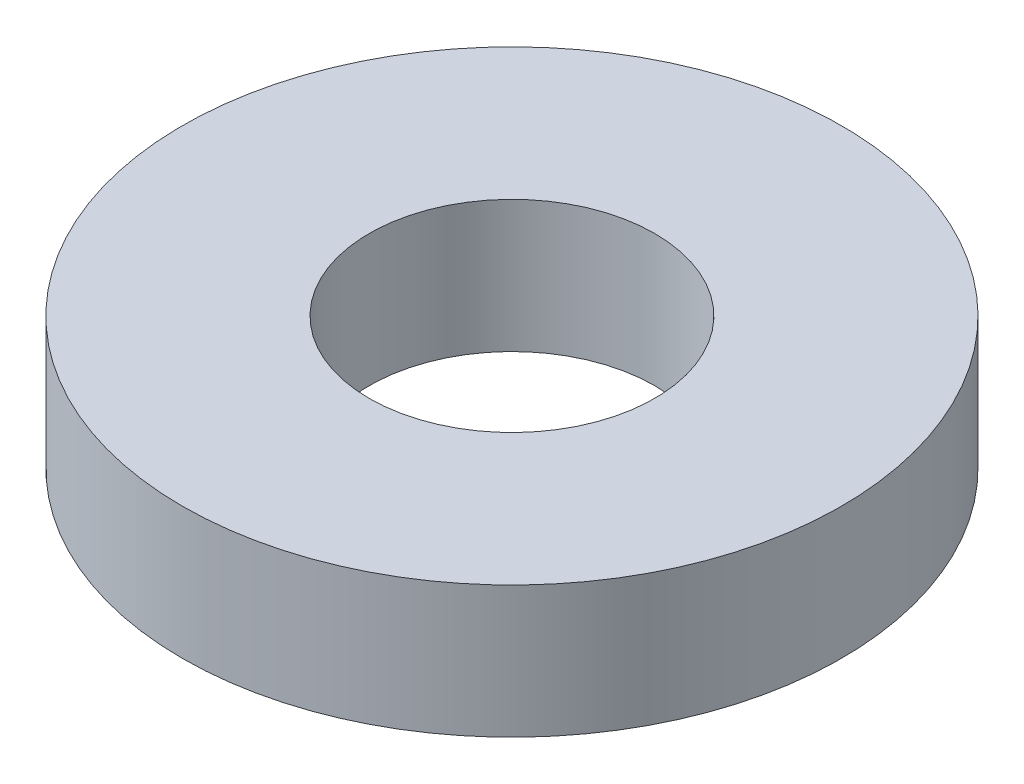
SolidWorks part; units mm, degrees
ref_plane "Front Plane" through (0, 0, 0) normal (0, 0, 1) x (1, 0, 0)
ref_plane "Top Plane" through (0, 0, 0) normal (0, 1, 0) x (1, 0, 0)
ref_plane "Right Plane" through (0, 0, 0) normal (1, 0, 0) x (0, 0, -1)
sketch "Sketch1" plane through (0, 0, 0) normal (0, 1, 0) x (1, 0, 0)
  circle A0 centre (0, 0) radius 1.651
  circle A1 centre (0, 0) radius 3.81
  dimension "D1" = 3.302
  dimension "D2" = 7.62
extrude "Boss-Extrude1" add sketch "Sketch1" along normal blind 1.524
